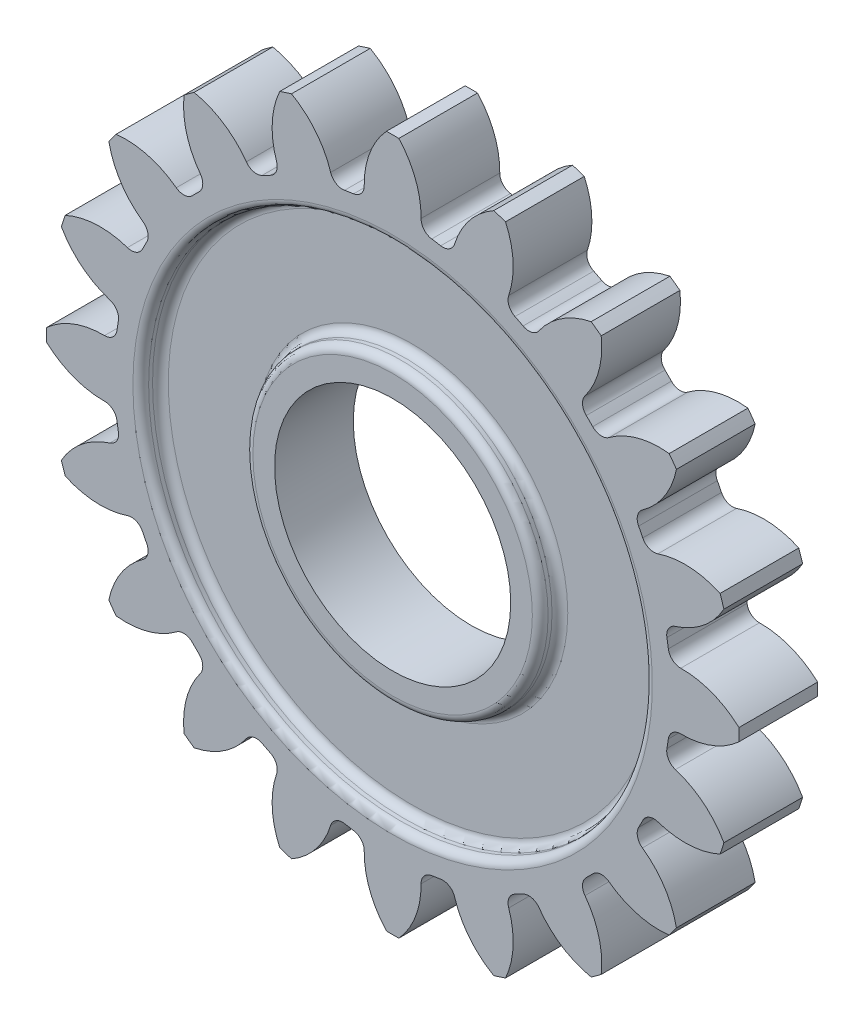
SolidWorks part; units mm, degrees
ref_plane "Front Plane" through (0, 0, 0) normal (0, 0, 1) x (1, 0, 0)
ref_plane "Top Plane" through (0, 0, 0) normal (0, 1, 0) x (1, 0, 0)
ref_plane "Right Plane" through (0, 0, 0) normal (1, 0, 0) x (0, 0, -1)
sketch "Sketch1" plane through (0, 0, 0) normal (0, 0, 1) x (1, 0, 0)
  line L0 (0, 0) -> (0, 27) construction
  line L1 (-40, 20) -> (40, 20) construction
  line L2 (-37.5877, 6.3192) -> (37.5877, 33.6808) construction
  line L3 (0, 0) -> (-13.6808, 37.5877) construction
  line L4 (-1.5708, 27) -> (1.5708, 27) construction
  line L5 (-1.5708, 27) -> (-1.5708, -9.7587) construction
  line L6 (1.5708, 27) -> (1.5708, 103.2413) construction
  circle A0 centre (0, 0) radius 20 construction
  circle A1 centre (0, 0) radius 22 construction
  circle A2 centre (0, 0) radius 17.6858 construction
  circle A3 centre (0, 0) radius 117.4616 construction
  circle A6 centre (-1.5708, 19.9382) radius 6.2832 construction
  circle A7 centre (4.5142, 18.0726) radius 6.2832 construction
  point P6 (0, 20)
  point P7 (0, 22)
  point P8 (0, 17.6858)
  point P12 (0, 20)
  point P15 (0, 20)
  point P21 (0, 27)
  point P25 (-1.5708, 19.9382)
  point P29 (-0.3931, 21.9965)
  point P32 (-1.7511, 17.5989)
  dimension "D1" = 40
  dimension "D2" = 44
  dimension "D3" = 35.3717
  dimension "D10" = 234.9232
  dimension "D12" = 12.5664
  dimension "D13" = 12.5664
  dimension "D4" = 80
  dimension "D5" = 20
  dimension "D6" = 27
  dimension "D7" = 40
  dimension "D8" = 20
  dimension "D11" = 3.1416
sketch "Sketch4" plane through (0, 0, 0) normal (0, 0, 1) x (1, 0, 0)
  line L0 (-1.5708, 19.9382) -> (1.5708, 20) construction
  line L1 (-40, 20) -> (40, 20) construction
  line L2 (1.5708, 27) -> (1.5708, 103.2413) construction
  line L3 (0, 20) -> (0, 22) construction
  line L4 (0, 0) -> (0, 27) construction
  arc A0 (-2.4808, 17.511) -> (2.4808, 17.511) centre (0, 0) ccw
  arc A1 (-1.8057, 18.2985) -> (-0.3931, 21.9965) centre (3.5644, 18.3659) cw
  arc A2 (1.8057, 18.2985) -> (0.3931, 21.9965) centre (-3.5644, 18.3659) ccw
  arc A3 (-0.3931, 21.9965) -> (0.3931, 21.9965) centre (0, 0) cw
  arc A4 (2.4808, 17.511) -> (1.8057, 18.2985) centre (2.591, 18.2886) cw
  arc A5 (-1.8057, 18.2985) -> (-2.4808, 17.511) centre (-2.591, 18.2886) cw
  point P21 (1.7511, 17.5989)
  point P29 (-1.7511, 17.5989)
  dimension "D1" = 0.7854
extrude "Boss-Extrude1" add sketch "Sketch4" along normal blind 5
pattern_circular "CirPattern1" count 20 over 360 about axis through (0, 0, 0) along (0, 0, 1) of bodies 101
sketch "Sketch5" plane through (0, 0, 5) normal (0, 0, 1) x (1, 0, 0)
  circle A0 centre (0, 0) radius 17.6858
  dimension "D1" = 35.3717
extrude "Boss-Extrude2" add sketch "Sketch5" against normal blind 5
sketch "Sketch6" plane through (0, 0, 5) normal (0, 0, 1) x (1, 0, 0)
  circle A0 centre (0, 0) radius 7.5
  dimension "D1" = 15
extrude "Cut-Extrude1" cut sketch "Sketch6" against normal blind 20
sketch "Sketch7" plane through (0, 0, 5) normal (0, 0, 1) x (1, 0, 0)
  circle A0 centre (0, 0) radius 16
  circle A1 centre (0, 0) radius 9.375
  dimension "D1" = 32
  dimension "D2" = 18.75
extrude "Cut-Extrude2" cut sketch "Sketch7" against normal blind 1.25
ref_plane "Plane1" through (0, 0, 2.5) normal (0, 0, 1) x (1, 0, 0)
mirror "Mirror1" about plane through (0, 0, 2.5) normal (0, 0, 1) of "Cut-Extrude2"
fillet "Fillet1" radius 0.5 8 edges at (16, 0, 3.75) (9.375, 0, 3.75) (16, 0, 5) (9.375, 0, 5) (16, 0, 1.25) (9.375, 0, 0) (16, 0, 0) (9.375, 0, 1.25)
equation "\"M\"= 2'Module"
equation "\"N\"= 20'Number of teeth"
equation "\"Ø\"= 20'Pressure Angle (20/24 deg)"
equation "\"CP\"= 3.14159 * \"M\"'Circular Pitch"
equation "\"Dpc\"= \"N\" * \"M\"'Diameter of Pitch Circle"
equation "\"t\"= \"CP\" / 2'Tooth Thickness"
equation "\"c\"= \"CP\" / 20'Clearence"
equation "\"r\"= \"CP\" / 8'Root Fillet Radius"
equation "\"a\"= \"M\"'Addentum"
equation "\"b\"= \"a\" + \"c\"'Deduntum"
equation "\"Da\"= \"Dpc\" + ( 2 * \"a\" )'Addentum circle Diameter"
equation "\"Db\"= \"Dpc\" - ( 2 * \"b\" )'Deduntum Circle Diameter"
equation "\"D1@Sketch1\"=\"Dpc\""
equation "\"D2@Sketch1\"=\"Da\""
equation "\"D3@Sketch1\"=\"Db\""
equation "\"D4@Sketch1\"=\"Dpc\"*2"
equation "\"D5@Sketch1\"=\"Ø\""
equation "\"D6@Sketch1\"=(\"Da\"/2)+5"
equation "\"D7@Sketch1\"=\"D4@Sketch1\"/2"
equation "\"D8@Sketch1\"=\"Ø\""
equation "\"D11@Sketch1\"=\"t\""
equation "\"D12@Sketch1\"=\"CP\"*2"
equation "\"D13@Sketch1\"= \"CP\" * 2"
equation "\"D1@Sketch4\"=\"r\""
equation "\"D1@CirPattern1\"=\"N\""
equation "\"H\"= 15'Central Hole"
equation "\"D1@Sketch6\"=\"H\""
equation "\"D1@Sketch5\"=\"Db\""
equation "\"T1\"= 5'Extrude Thickness"
equation "\"D1@Boss-Extrude1\"=\"T1\""
equation "\"D1@Boss-Extrude2\"=\"T1\""
equation "\"D1@Cut-Extrude2\"=\"T1\"/4"
equation "\"D1@Fillet1\"=0.5"
equation "\"D1@Sketch7\"=\"Dpc\"*0.8"
equation "\"D2@Sketch7\"=\"H\"*1.25"
